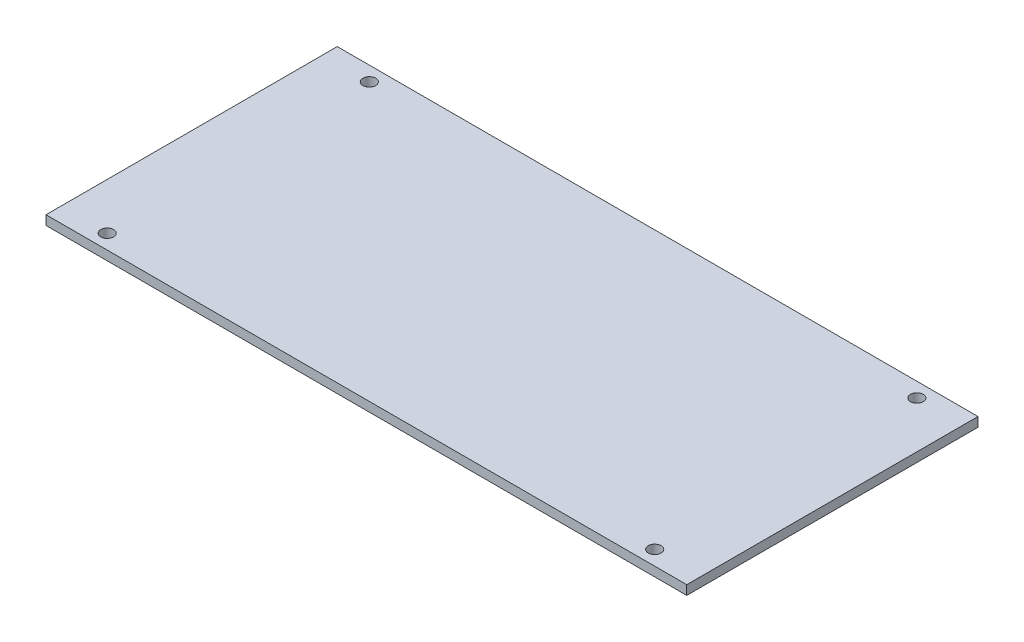
SolidWorks part; units mm, degrees
material "Acrylic (Medium-high impact)"
ref_plane "Front Plane" through (0, 0, 0) normal (0, 0, 1) x (1, 0, 0)
ref_plane "Top Plane" through (0, 0, 0) normal (0, 1, 0) x (1, 0, 0)
ref_plane "Right Plane" through (0, 0, 0) normal (1, 0, 0) x (0, 0, -1)
sketch "Sketch1" plane through (0, 0, 0) normal (0, 1, 0) x (1, 0, 0)
  line L1 (-69.85, -31.75) -> (69.85, -31.75)
  line L2 (-69.85, -31.75) -> (-69.85, 31.75)
  line L3 (-69.85, 31.75) -> (69.85, 31.75)
  line L4 (69.85, -31.75) -> (69.85, 31.75)
  line L5 (-69.85, -31.75) -> (69.85, 31.75) construction
  line L6 (-69.85, 31.75) -> (69.85, -31.75) construction
  point P0 (0, 0)
  dimension "D1" = 139.7
  dimension "D2" = 63.5
extrude "Boss-Extrude1" add sketch "Sketch1" along normal blind 2.032
sketch "Sketch2" plane through (0, 2.032, 0) normal (0, 1, 0) x (1, 0, 0)
  line L0 (0, 0) -> (0, 31.75) construction
  line L1 (69.85, 31.75) -> (-69.85, 31.75) construction
  line L2 (0, 0) -> (69.85, 0) construction
  line L3 (69.85, -31.75) -> (69.85, 31.75) construction
  line L4 (69.85, 28.575) -> (59.69, 28.575) construction
  circle A0 centre (59.69, 28.575) radius 1.397
  circle A1 centre (-59.69, 28.575) radius 1.397
  circle A2 centre (59.69, -28.575) radius 1.397
  circle A3 centre (-59.69, -28.575) radius 1.397
  dimension "D3" = 2.794
  dimension "D1" = 10.16
  dimension "D2" = 3.175
extrude "Cut-Extrude1" cut sketch "Sketch2" against normal through all
